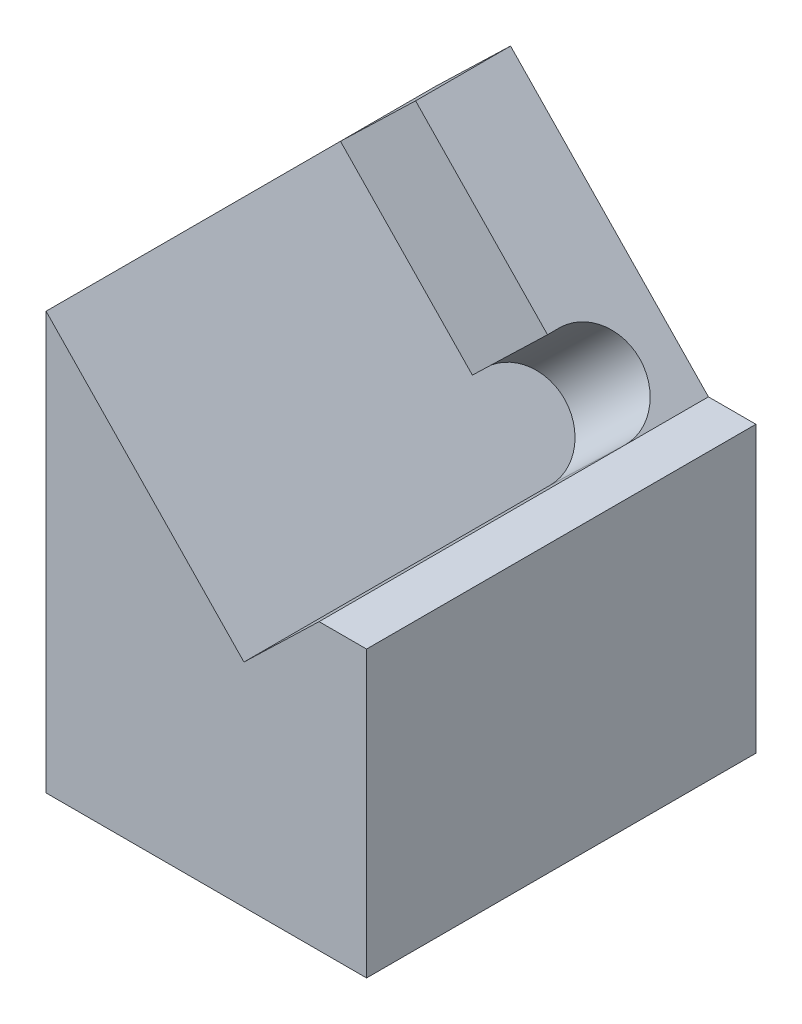
SolidWorks part; units mm, degrees
ref_plane "Front Plane" through (0, 0, 0) normal (0, 0, 1) x (1, 0, 0)
ref_plane "Top Plane" through (0, 0, 0) normal (0, 1, 0) x (1, 0, 0)
ref_plane "Right Plane" through (0, 0, 0) normal (1, 0, 0) x (0, 0, -1)
sketch "Sketch1" plane through (0, 0, 0) normal (0, 0, 1) x (1, 0, 0)
  line L0 (0, 0) -> (0, 4.7873)
  line L1 (0, 4.7873) -> (1.5825, 6.3155)
  line L2 (1.5825, 6.3155) -> (5.75, 2)
  line L3 (5.75, 2) -> (6.75, 2)
  line L4 (6.75, 2) -> (6.75, 0)
  line L5 (6.75, 0) -> (0, 0)
  dimension "D1" = 6.75
  dimension "D2" = 2
  dimension "D3" = 1
  dimension "D4" = 134
  dimension "D5" = 2.2
extrude "Boss-Extrude1" add sketch "Sketch1" along normal blind 8.2
sketch "Sketch2" plane through (3.9747, 3.8383, 0) normal (0.7193, 0.6947, 0) x (0, 0, -1)
  line L1 (-8.2, 3.4437) -> (-2, 3.4437)
  line L2 (-8.2, 3.4437) -> (-8.2, -2.5556)
  line L3 (-8.2, -2.5556) -> (-1.75, -2.5556)
  line L4 (-2, 3.4437) -> (-2, -0.5556)
  line L5 (-8.2, -2.5556) -> (0, -2.5556) construction
  line L6 (-2, -0.5556) -> (-1.75, -0.5556)
  line L8 (0, -2.5556) -> (0, 3.4437) construction
  arc A1 (-1.75, -2.5556) -> (-1.75, -0.5556) centre (-1.75, -1.5556) ccw
  dimension "D2" = 1
  dimension "D1" = 0.25
  dimension "D4" = 2
extrude "Cut-Extrude1" cut sketch "Sketch2" against normal blind 2.2
sketch "Sketch3" plane through (0, 0, 0) normal (0, -1, 0) x (1, 0, 0)
  line L1 (0, 8.2) -> (6.75, 8.2)
  line L2 (0, 8.2) -> (0, 0)
  line L3 (0, 0) -> (6.75, 0)
  line L4 (6.75, 8.2) -> (6.75, 0)
extrude "Boss-Extrude2" add sketch "Sketch3" along normal blind 4
hole_wizard "Ø1.5mm Dowel Hole1" positions "Sketch6" profile "Sketch4" hole size "Ø1.5" standard "ISO"
sketch "Sketch6" plane through (0, -4, 0) normal (0, -1, 0) x (-1, 0, 0)
  line L0 (0, -8.2) -> (0, 0) construction
  point P0 (-2, -7.1)
  point P2 (-2, -1.1)
  point P5 (0, -4.1)
  dimension "D1" = 6
  dimension "D2" = 3
  dimension "D3" = 2
sketch "Sketch4" plane through (2, -4, 7.1) normal (1, 0, 0) x (0, 0, -1)
  line L0 (0, 0) -> (0, 3.4506)
  line L1 (0, 3.4506) -> (0.75, 3)
  line L2 (0.75, 3) -> (0.75, 0)
  line L5 (0.75, 0) -> (0, 0)
  line L10 (0, 3.4506) -> (-0.75, 3) construction
  line L11 (0, -6.35) -> (0, 107.95) construction
  dimension "Hole Dia." = 1.5
  dimension "Hole Depth" = 3
  dimension "Drill Angle" = 118
hole_wizard "M2x0.4 Tapped Hole1" positions "Sketch8" profile "Sketch7" tap size "M2x0.4" standard "ANSI Metric"
sketch "Sketch8" plane through (0, -4, 0) normal (0, -1, 0) x (-1, 0, 0)
  line L0 (0, -8.2) -> (0, 0) construction
  line L1 (0, 0) -> (-6.75, 0) construction
  point P0 (-2, -4.1)
  dimension "D1" = 2
  dimension "D2" = 4.1
sketch "Sketch7" plane through (2, -4, 4.1) normal (1, 0, 0) x (0, 0, -1)
  line L0 (0, 0) -> (0, 4.4807)
  line L1 (0, 4.4807) -> (0.8, 4)
  line L2 (0.8, 4) -> (0.8, 0)
  line L5 (0.8, 0) -> (0, 0)
  line L10 (0, 4.4807) -> (-0.8, 4) construction
  line L11 (0, -6.35) -> (0, 107.95) construction
  dimension "Tap Drill Dia." = 1.6
  dimension "Tap Drill Depth" = 4
  dimension "Drill Angle" = 118
cosmetic thread "Hole Thread1" parameters "D1"=3.5, "D2"=2
